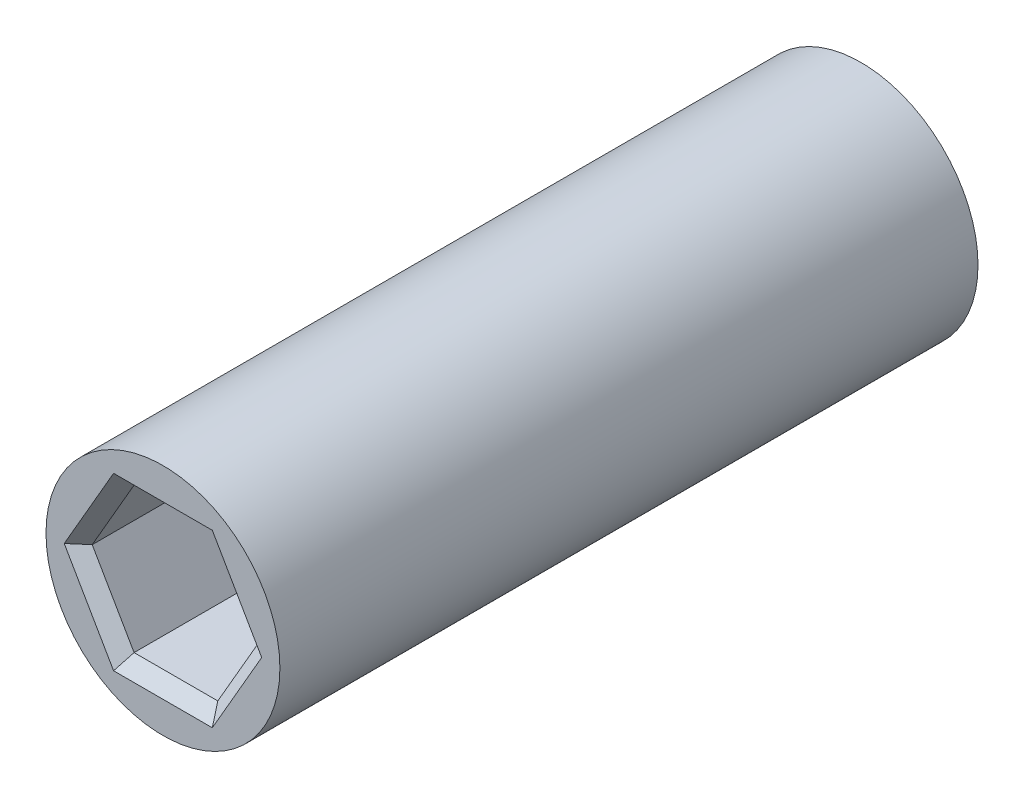
SolidWorks part; units mm, degrees
ref_plane "Front Plane" through (0, 0, 0) normal (0, 0, 1) x (1, 0, 0)
ref_plane "Top Plane" through (0, 0, 0) normal (0, 1, 0) x (1, 0, 0)
ref_plane "Right Plane" through (0, 0, 0) normal (1, 0, 0) x (0, 0, -1)
sketch "Sketch1" plane through (0, 0, 0) normal (0, 1, 0) x (1, 0, 0)
  line L0 (0, 0) -> (0, 61.86) construction
  line L1 (0, 44.36) -> (0, 17.5)
  point P3 (0, 37.86)
  point P4 (0, 24)
  point P5 (0, 44.36)
  point P6 (0, 17.5)
  dimension "D1" = 61.86
  dimension "D2" = 24
  dimension "D3" = 24
  dimension "D4" = 13.86
  dimension "D5" = 6.5
  dimension "D6" = 6.5
revolve "Revolve-Thin1" add sketch "Sketch1" angle 360 about L0 wall 4.5
sketch "Sketch2" plane through (0, 0, -17.5) normal (0, 0, 1) x (1, 0, 0)
  line L1 (1.6108, 2.79) -> (-1.6108, 2.79)
  line L2 (-1.6108, 2.79) -> (-3.2216, 0)
  line L3 (-3.2216, 0) -> (-1.6108, -2.79)
  line L4 (-1.6108, -2.79) -> (1.6108, -2.79)
  line L5 (1.6108, -2.79) -> (3.2216, 0)
  line L6 (3.2216, 0) -> (1.6108, 2.79)
  circle A0 centre (0, 0) radius 2.79 construction
  dimension "D1" = 5.58
extrude "Cut-Extrude1" cut sketch "Sketch2" against normal blind 7
sketch "Sketch3" plane through (0, 0, -44.36) normal (0, 0, -1) x (-1, 0, 0)
  line L1 (1.6108, 2.79) -> (-1.6108, 2.79)
  line L2 (-1.6108, 2.79) -> (-3.2216, 0)
  line L3 (-3.2216, 0) -> (-1.6108, -2.79)
  line L4 (-1.6108, -2.79) -> (1.6108, -2.79)
  line L5 (1.6108, -2.79) -> (3.2216, 0)
  line L6 (3.2216, 0) -> (1.6108, 2.79)
  circle A0 centre (0, 0) radius 2.79 construction
  dimension "D1" = 5.58
extrude "Cut-Extrude2" cut sketch "Sketch3" against normal blind 7
chamfer "Chamfer1" distance 0.5 angle 45 12 edges at (2.4162, 1.395, -17.5) (2.4162, -1.395, -17.5) (0, -2.79, -17.5) (-2.4162, -1.395, -17.5) (-2.4162, 1.395, -17.5) (0, 2.79, -17.5) (0, 2.79, -44.36) (-2.4162, 1.395, -44.36) (-2.4162, -1.395, -44.36) (0, -2.79, -44.36) (2.4162, -1.395, -44.36) (2.4162, 1.395, -44.36)
sketch3d "3DSketch1" plane through (0, 0, 0) normal (0, 0, 1) x (1, 0, 0)
sketch "Sketch4" plane through (0, -4.5, 0) normal (0, 1, 0) x (1, 0, 0)
  line L0 (-4.5, 17.5) -> (4.5, 17.5) construction
  line L1 (4.5, 44.36) -> (-4.5, 44.36) construction
  line L2 (-4.5, 17.5) -> (4.5, 17.5) construction
  line L3 (4.5, 44.36) -> (-4.5, 44.36) construction
  line L4 (-4.5, 17.5) -> (-4.5, 44.36) construction
  line L5 (4.5, 44.36) -> (4.5, 17.5) construction
  line L6 (-4.5, 30.93) -> (4.5, 30.93) construction
  text T0 "<b><i>R</i></b>"
extrude "Cut-Extrude3" cut sketch "Sketch4" along normal blind 1
